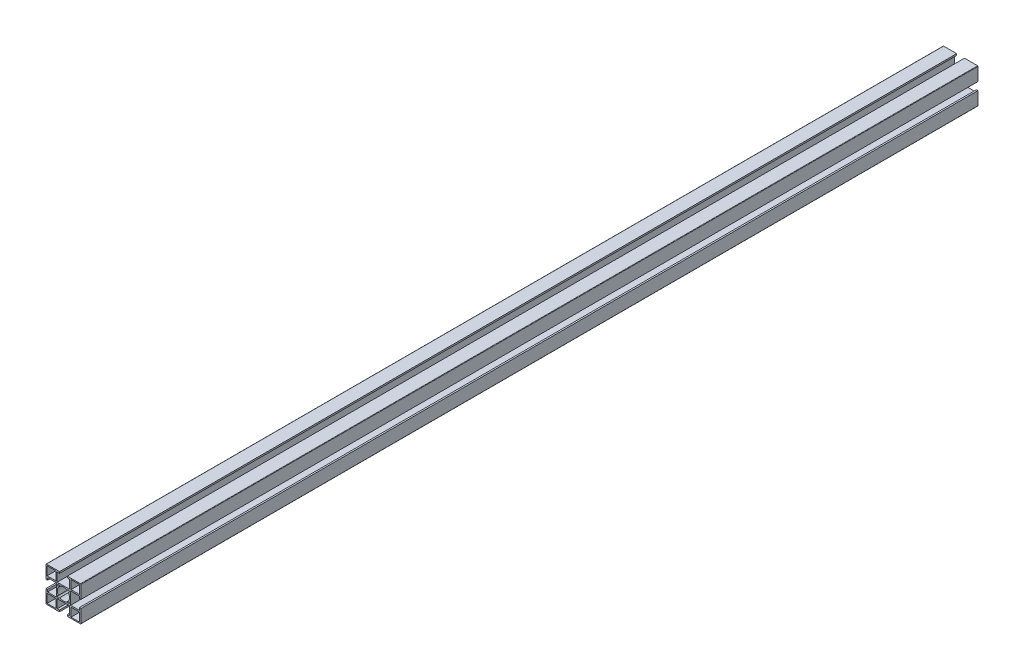
SolidWorks part; units mm, degrees
ref_plane "前视基准面" through (0, 0, 0) normal (0, 0, 1) x (1, 0, 0)
ref_plane "上视基准面" through (0, 0, 0) normal (0, 1, 0) x (1, 0, 0)
ref_plane "右视基准面" through (0, 0, 0) normal (1, 0, 0) x (0, 0, -1)
other "Configuration Table"
sketch "草图1" plane through (0, 0, 0) normal (1, 0, 0) x (0, 0, -1)
  line L0 (0, 0) -> (1030, 0)
  dimension "D1" = 1030
other "铝型材 40 X 40A X R0.5(1)"
ref_plane "基准面1" through (0, 0, 0) normal (0, 0, -1) x (0, 1, 0)
sketch "Sketch1" plane through (0, 0, 0) normal (0, 0, -1) x (0, 1, 0)
  line L0 (0, 0) -> (0, 16.3773) construction
  line L1 (0, 0) -> (-5.6569, 5.6569) construction
  line L2 (-19.5, 20) -> (-4.5, 20)
  line L3 (-20, 19.5) -> (-20, 4.5)
  line L4 (-19.5, -20) -> (-4.5, -20)
  line L5 (20, 19.5) -> (20, 4.5)
  line L6 (-4.879, 6.4347) -> (-4.1104, 5.6661)
  line L7 (-6.4347, 4.879) -> (-5.6661, 4.1104)
  line L8 (6.4347, 4.879) -> (5.6661, 4.1104)
  line L9 (0, 0) -> (20, 0) construction
  line L10 (4.879, 6.4347) -> (4.1104, 5.6661)
  line L11 (4.879, -6.4347) -> (4.1104, -5.6661)
  line L12 (6.4347, -4.879) -> (5.6661, -4.1104)
  line L13 (-6.4347, -4.879) -> (-5.6661, -4.1104)
  line L14 (-4.879, -6.4347) -> (-4.1104, -5.6661)
  line L15 (-4.5, 20) -> (-4.5, 18.2)
  line L16 (-18.7, 18.7) -> (-8.7, 18.7)
  line L17 (-18.7, 18.7) -> (-18.7, 8.7)
  line L18 (-18.7, 8.7) -> (-8.7, 8.7)
  line L19 (-8.7, 18.7) -> (-8.7, 8.7)
  line L20 (-7.1, 18.2) -> (-4.5, 18.2)
  line L21 (-7.1, 18.2) -> (-7.1, 8.2)
  line L22 (-7.1, 8.2) -> (7.1, 8.2)
  line L23 (7.1, 18.2) -> (7.1, 8.2)
  line L24 (4.5, 20) -> (4.5, 18.2)
  line L25 (4.5, 20) -> (19.5, 20)
  line L26 (4.5, 18.2) -> (7.1, 18.2)
  line L27 (8.7, 18.7) -> (8.7, 8.7)
  line L28 (18.7, 8.7) -> (8.7, 8.7)
  line L29 (18.7, 18.7) -> (18.7, 8.7)
  line L30 (18.7, 18.7) -> (8.7, 18.7)
  line L31 (18.2, 7.1) -> (8.2, 7.1)
  line L32 (18.2, 7.1) -> (18.2, 4.5)
  line L33 (20, 4.5) -> (18.2, 4.5)
  line L34 (8.2, 7.1) -> (8.2, -7.1)
  line L35 (18.2, -7.1) -> (8.2, -7.1)
  line L36 (18.2, -4.5) -> (18.2, -7.1)
  line L37 (20, -4.5) -> (18.2, -4.5)
  line L38 (7.1, -18.2) -> (7.1, -8.2)
  line L39 (7.1, -18.2) -> (4.5, -18.2)
  line L40 (4.5, -20) -> (4.5, -18.2)
  line L41 (7.1, -8.2) -> (-7.1, -8.2)
  line L42 (-7.1, -18.2) -> (-7.1, -8.2)
  line L43 (-4.5, -18.2) -> (-7.1, -18.2)
  line L44 (-4.5, -20) -> (-4.5, -18.2)
  line L45 (-18.2, -7.1) -> (-8.2, -7.1)
  line L46 (-18.2, -7.1) -> (-18.2, -4.5)
  line L47 (-20, -4.5) -> (-18.2, -4.5)
  line L48 (-8.2, -7.1) -> (-8.2, 7.1)
  line L49 (-18.2, 7.1) -> (-8.2, 7.1)
  line L50 (-18.2, 4.5) -> (-18.2, 7.1)
  line L51 (-20, 4.5) -> (-18.2, 4.5)
  line L52 (4.5, -20) -> (19.5, -20)
  line L53 (-20, -4.5) -> (-20, -19.5)
  line L54 (20, -4.5) -> (20, -19.5)
  line L55 (18.7, -18.7) -> (18.7, -8.7)
  line L56 (18.7, -8.7) -> (8.7, -8.7)
  line L57 (8.7, -18.7) -> (8.7, -8.7)
  line L58 (18.7, -18.7) -> (8.7, -18.7)
  line L59 (-8.7, -18.7) -> (-8.7, -8.7)
  line L60 (-18.7, -8.7) -> (-8.7, -8.7)
  line L61 (-18.7, -18.7) -> (-8.7, -18.7)
  line L62 (-18.7, -18.7) -> (-18.7, -8.7)
  arc A0 (-4.1104, 5.6661) -> (4.1104, 5.6661) centre (0, 0) cw
  arc A1 (-4.879, 6.4347) -> (-6.4347, 4.879) centre (-5.6569, 5.6569) ccw
  arc A2 (-4.1104, -5.6661) -> (4.1104, -5.6661) centre (0, 0) ccw
  arc A3 (-5.6661, 4.1104) -> (-5.6661, -4.1104) centre (0, 0) ccw
  arc A4 (6.4347, 4.879) -> (4.879, 6.4347) centre (5.6569, 5.6569) ccw
  arc A5 (4.879, -6.4347) -> (6.4347, -4.879) centre (5.6569, -5.6569) ccw
  arc A6 (-6.4347, -4.879) -> (-4.879, -6.4347) centre (-5.6569, -5.6569) ccw
  arc A7 (5.6661, 4.1104) -> (5.6661, -4.1104) centre (0, 0) cw
  arc A8 (-19.5, 20) -> (-20, 19.5) centre (-19.5, 19.5) ccw
  arc A9 (19.5, 20) -> (20, 19.5) centre (19.5, 19.5) cw
  arc A10 (19.5, -20) -> (20, -19.5) centre (19.5, -19.5) ccw
  arc A11 (-20, -19.5) -> (-19.5, -20) centre (-19.5, -19.5) ccw
  point P86 (20, 20)
  point P87 (-20, 20)
  point P88 (-20, -20)
  point P89 (20, -20)
  point P90 (0, 0)
  dimension "D2" = 7
  dimension "D3" = 45
  dimension "D4" = 1.1
  dimension "D5" = 1.8
  dimension "D6" = 8
  dimension "D7" = 1.3
  dimension "D8" = 14.2
  dimension "D10" = 10
  dimension "D11" = 10
  dimension "D12" = 40
  dimension "D13" = 9
  dimension "D14" = 0.5
  dimension "D9" = 1.3
sketch "草图2" plane through (8.2, 0, 0) normal (1, 0, 0) x (0, 0, -1)
  line L0 (0, 0) -> (1030, 0) construction
  line L1 (0, 7.1) -> (0, -7.1) construction
  circle A0 centre (40, 0) radius 2.5
  dimension "D1" = 40
extrude "切除-拉伸1" cut sketch "草图2" against normal through all
